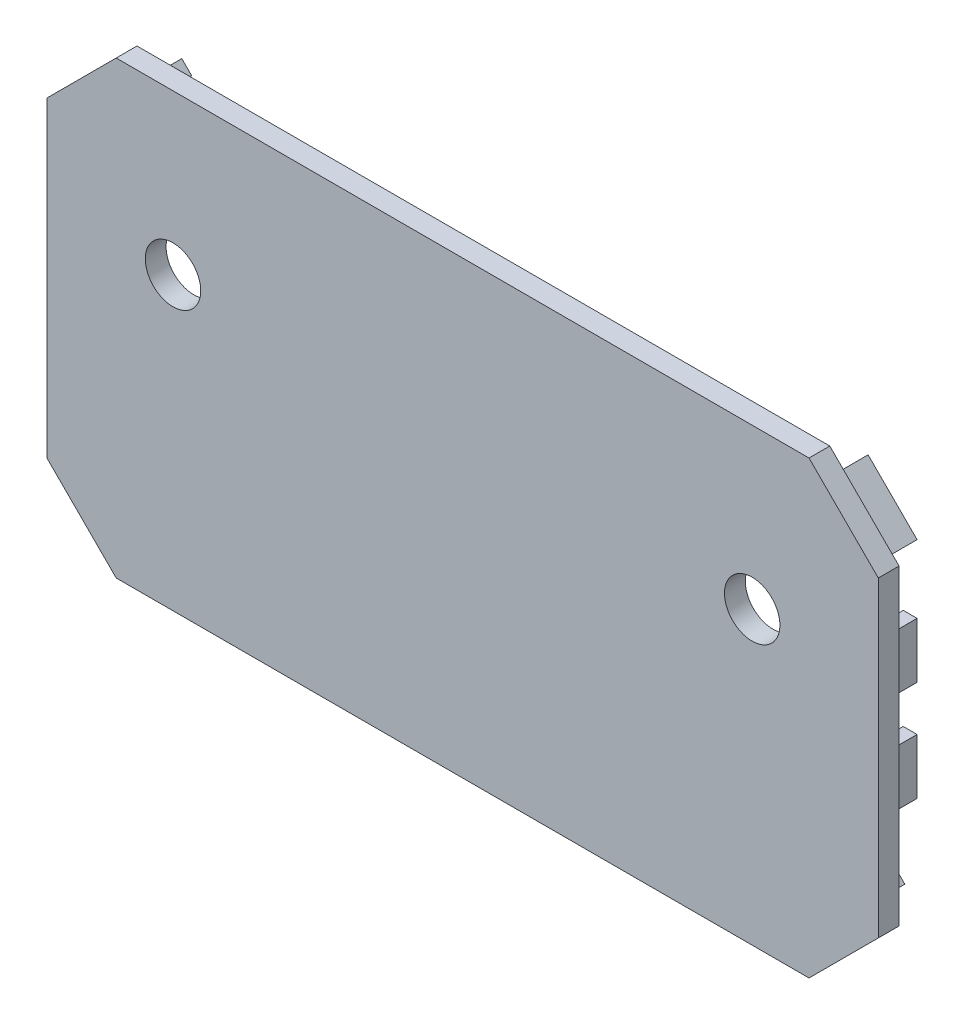
SolidWorks part; units mm, degrees
ref_plane "Front Plane" through (0, 0, 0) normal (0, 0, 1) x (1, 0, 0)
ref_plane "Top Plane" through (0, 0, 0) normal (0, 1, 0) x (1, 0, 0)
ref_plane "Right Plane" through (0, 0, 0) normal (1, 0, 0) x (0, 0, -1)
sketch "Sketch1" plane through (0, 0, 0) normal (0, 0, 1) x (1, 0, 0)
  line L1 (0, 0) -> (120, 0)
  line L2 (0, 0) -> (0, 65)
  line L3 (0, 65) -> (120, 65)
  line L4 (120, 0) -> (120, 65)
  dimension "D1" = 65
  dimension "D2" = 120
extrude "Boss-Extrude1" add sketch "Sketch1" along normal blind 3
chamfer "Chamfer1" distance 10 angle 45 4 edges at (0, 0, 1.5) (0, 65, 1.5) (120, 0, 1.5) (120, 65, 1.5)
sketch "Sketch2" plane through (0, 0, 0) normal (0, 0, -1) x (-1, 0, 0)
  line L0 (-116.6, 29.2426) -> (-114.6, 29.2426)
  line L1 (-116.6, 43.7574) -> (-114.6, 43.7574)
  line L2 (-116.6, 43.7574) -> (-116.6, 35.7574)
  line L3 (-116.6, 35.7574) -> (-114.6, 35.7574)
  line L4 (-114.6, 43.7574) -> (-114.6, 35.7574)
  line L9 (-116.6, 29.2426) -> (-116.6, 21.2426)
  line L10 (-116.6, 21.2426) -> (-114.6, 21.2426)
  line L11 (-114.6, 29.2426) -> (-114.6, 21.2426)
  line L17 (-117, 53.7574) -> (-117, 11.2426) construction
  line L18 (-109.5289, 60.6627) -> (-116.6, 53.5917)
  line L19 (-116.6, 53.5917) -> (-115.1858, 52.1775)
  line L20 (-115.1858, 52.1775) -> (-108.1147, 59.2485)
  line L21 (-108.1147, 59.2485) -> (-109.5289, 60.6627)
  line L22 (-108.7574, 62) -> (-117, 53.7574) construction
  line L30 (-117, 53.7574) -> (-115, 52.9289) construction
  line L32 (-60, 65) -> (-60, 86.5119) construction
  line L33 (-110, 65) -> (-10, 65) construction
  line L38 (-11.8853, 59.2485) -> (-10.4711, 60.6627)
  line L39 (-4.8142, 52.1775) -> (-11.8853, 59.2485)
  line L40 (-3.4, 53.5917) -> (-4.8142, 52.1775)
  line L41 (-10.4711, 60.6627) -> (-3.4, 53.5917)
  line L46 (-5.4, 29.2426) -> (-5.4, 21.2426)
  line L47 (-3.4, 21.2426) -> (-5.4, 21.2426)
  line L48 (-3.4, 29.2426) -> (-3.4, 21.2426)
  line L49 (-5.4, 43.7574) -> (-5.4, 35.7574)
  line L50 (-3.4, 35.7574) -> (-5.4, 35.7574)
  line L51 (-3.4, 43.7574) -> (-3.4, 35.7574)
  line L52 (-3.4, 43.7574) -> (-5.4, 43.7574)
  line L53 (-3.4, 29.2426) -> (-5.4, 29.2426)
  line L56 (-114.8343, 9.6426) -> (-113.4201, 11.0569)
  line L58 (-113.4201, 11.0569) -> (-107.7632, 5.4)
  line L59 (-107.7632, 5.4) -> (-95.7632, 5.4)
  line L60 (-95.7632, 5.4) -> (-95.7632, 3.4)
  line L61 (-95.7632, 3.4) -> (-108.5917, 3.4)
  line L62 (-108.7574, 3) -> (-107.9289, 5) construction
  line L63 (-108.5917, 3.4) -> (-114.8343, 9.6426)
  line L64 (-120, 10) -> (-110, 0) construction
  line L65 (-117, 11.2426) -> (-108.7574, 3) construction
  line L67 (-11.4083, 3.4) -> (-5.1657, 9.6426)
  line L68 (-24.2368, 3.4) -> (-11.4083, 3.4)
  line L69 (-24.2368, 5.4) -> (-24.2368, 3.4)
  line L70 (-12.2368, 5.4) -> (-24.2368, 5.4)
  line L71 (-6.5799, 11.0569) -> (-12.2368, 5.4)
  line L72 (-5.1657, 9.6426) -> (-6.5799, 11.0569)
  dimension "D2" = 0.4
  dimension "D3" = 0.4
  dimension "D4" = 0.4
  dimension "D5" = 2
  dimension "D6" = 2
  dimension "D7" = 2
  dimension "D8" = 0.4
  dimension "D9" = 2
  dimension "D10" = 8
  dimension "D11" = 10
  dimension "D12" = 10
  dimension "D13" = 10
  dimension "D14" = 8
  dimension "D15" = 8
  dimension "D16" = 12
  dimension "D17" = 2
extrude "Boss-Extrude3" add sketch "Sketch2" along normal blind 6
chamfer "Chamfer2" distance 4 angle 45 10 edges at (101.7632, 5.4, 0) (110.5917, 8.2284, 0) (114.6, 25.2426, 0) (114.6, 39.7574, 0) (111.6503, 55.713, 0) (9.4083, 8.2284, 0) (18.2368, 5.4, 0) (5.4, 25.2426, 0) (5.4, 39.7574, 0) (8.3497, 55.713, 0)
sketch "Sketch4" plane through (0, 0, 0) normal (0, 0, -1) x (-1, 0, 0)
  line L0 (-24.4, 48) -> (-12, 48) construction
  line L1 (-24.4, 28.6) -> (-24.4, 48) construction
  line L3 (-60, 65) -> (-60, 75.3194) construction
  line L4 (-110, 65) -> (-10, 65) construction
  circle A0 centre (-18.2, 42) radius 4
  circle A1 centre (-101.8, 42) radius 4
  dimension "D1" = 8
  dimension "D2" = 6
  dimension "D3" = 6.2
extrude "Cut-Extrude1" cut sketch "Sketch4" against normal blind 6
